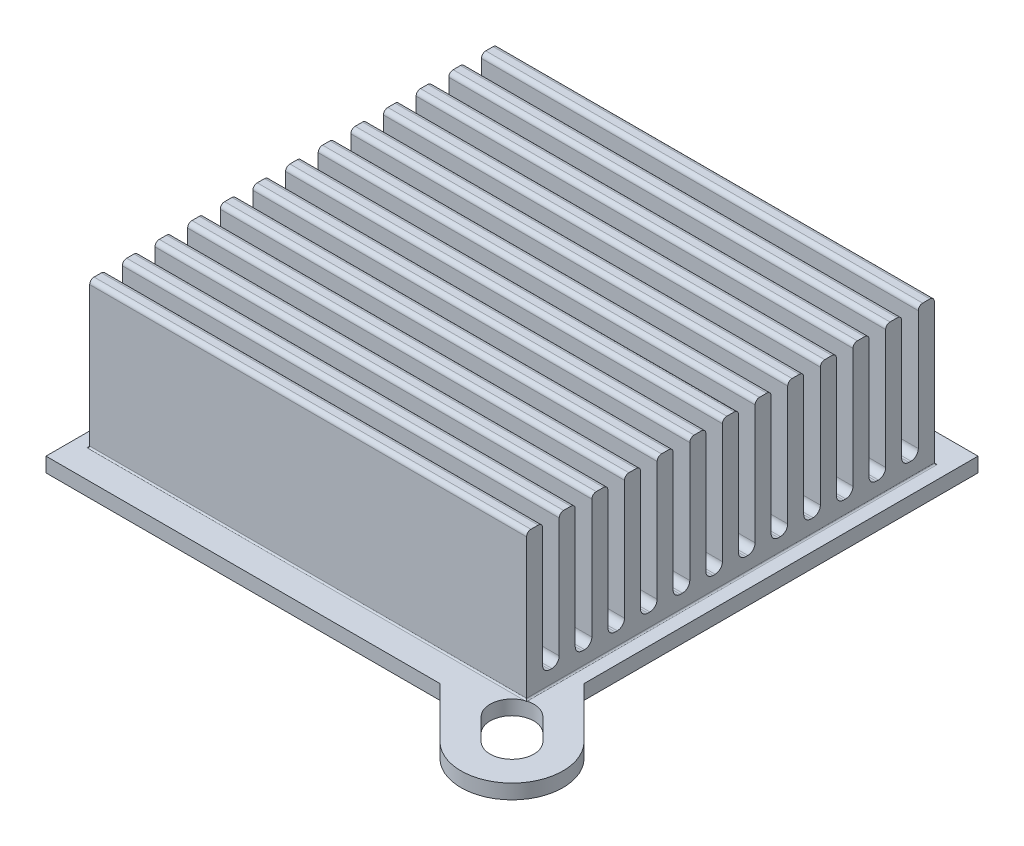
SolidWorks part; units mm, degrees
ref_plane "Płaszczyzna przednia" through (0, 0, 0) normal (0, 0, 1) x (1, 0, 0)
ref_plane "Płaszczyzna górna" through (0, 0, 0) normal (0, 1, 0) x (1, 0, 0)
ref_plane "Płaszczyzna prawa" through (0, 0, 0) normal (1, 0, 0) x (0, 0, -1)
sketch "Szkic1" plane through (0, 0, 0) normal (0, 1, 0) x (1, 0, 0)
  line L5 (-16, -16) -> (16, -16)
  line L6 (-16, -16) -> (-16, 16)
  line L7 (-16, 16) -> (16, 16)
  line L8 (16, -16) -> (16, 16)
  line L9 (-16, -16) -> (16, 16) construction
  line L10 (-16, 16) -> (16, -16) construction
  line L14 (-19.4454, 19.4454) -> (-5.5675, 33.3234) construction
  line L15 (19.4454, -19.4454) -> (38.3948, -0.496) construction
  line L16 (-19.4454, 19.4454) -> (19.4454, -19.4454) construction
  line L17 (-14.4957, 19.4454) -> (19.4454, -14.4957)
  line L18 (-19.4454, 14.4957) -> (14.4957, -19.4454)
  arc A2 (-14.4957, 19.4454) -> (-19.4454, 14.4957) centre (-16.9706, 16.9706) ccw
  arc A3 (14.4957, -19.4454) -> (19.4454, -14.4957) centre (16.9706, -16.9706) ccw
  point P0 (0, 0)
  dimension "D5" = 7
  dimension "D6" = 7
  dimension "D1" = 32
  dimension "D2" = 32
  dimension "D3" = 55
  dimension "D4" = 27.5
extrude "Dodanie-wyciągnięcie2" add sketch "Szkic1" along normal blind 1
sketch "Szkic2" plane through (0, 1, 0) normal (0, 1, 0) x (1, 0, 0)
  line L0 (-16, -16) -> (-16, 11.0503) construction
  line L1 (-15, 12.9) -> (15, 12.9)
  line L2 (-15, 12.9) -> (-15, 14)
  line L3 (-15, 14) -> (15, 14)
  line L4 (15, 12.9) -> (15, 14)
  line L5 (-15, 11.7583) -> (15, 11.7583)
  line L6 (-15, 10.6583) -> (15, 10.6583)
  line L7 (-15, 10.6583) -> (-15, 11.7583)
  line L8 (15, 10.6583) -> (15, 11.7583)
  line L9 (-15, 9.5167) -> (15, 9.5167)
  line L10 (-15, 8.4167) -> (15, 8.4167)
  line L11 (-15, 8.4167) -> (-15, 9.5167)
  line L12 (15, 8.4167) -> (15, 9.5167)
  line L13 (-15, 7.275) -> (15, 7.275)
  line L14 (-15, 6.175) -> (15, 6.175)
  line L15 (-15, 6.175) -> (-15, 7.275)
  line L16 (15, 6.175) -> (15, 7.275)
  line L17 (-15, 5.0333) -> (15, 5.0333)
  line L18 (-15, 3.9333) -> (15, 3.9333)
  line L19 (-15, 3.9333) -> (-15, 5.0333)
  line L20 (15, 3.9333) -> (15, 5.0333)
  line L21 (-15, 2.7917) -> (15, 2.7917)
  line L22 (-15, 1.6917) -> (15, 1.6917)
  line L23 (-15, 1.6917) -> (-15, 2.7917)
  line L24 (15, 1.6917) -> (15, 2.7917)
  line L25 (-15, 0.55) -> (15, 0.55)
  line L26 (-15, -0.55) -> (15, -0.55)
  line L27 (-15, -0.55) -> (-15, 0.55)
  line L28 (15, -0.55) -> (15, 0.55)
  line L29 (-15, -1.6917) -> (15, -1.6917)
  line L30 (-15, -2.7917) -> (15, -2.7917)
  line L31 (-15, -2.7917) -> (-15, -1.6917)
  line L32 (15, -2.7917) -> (15, -1.6917)
  line L33 (-15, -3.9333) -> (15, -3.9333)
  line L34 (-15, -5.0333) -> (15, -5.0333)
  line L35 (-15, -5.0333) -> (-15, -3.9333)
  line L36 (15, -5.0333) -> (15, -3.9333)
  line L37 (-15, -6.175) -> (15, -6.175)
  line L38 (-15, -7.275) -> (15, -7.275)
  line L39 (-15, -7.275) -> (-15, -6.175)
  line L40 (15, -7.275) -> (15, -6.175)
  line L41 (-15, -8.4167) -> (15, -8.4167)
  line L42 (-15, -9.5167) -> (15, -9.5167)
  line L43 (-15, -9.5167) -> (-15, -8.4167)
  line L44 (15, -9.5167) -> (15, -8.4167)
  line L45 (-15, -10.6583) -> (15, -10.6583)
  line L46 (-15, -11.7583) -> (15, -11.7583)
  line L47 (-15, -11.7583) -> (-15, -10.6583)
  line L48 (15, -11.7583) -> (15, -10.6583)
  line L49 (-15, -12.9) -> (15, -12.9)
  line L50 (-15, -14) -> (15, -14)
  line L51 (-15, -14) -> (-15, -12.9)
  line L52 (15, -14) -> (15, -12.9)
  line L53 (-11.0503, 16) -> (16, 16) construction
  line L54 (-16, -16) -> (11.0503, -16) construction
  dimension "D1" = 30
  dimension "D2" = 1
  dimension "D3" = 1.1
  dimension "D5" = 2
  dimension "D6" = 2
  dimension "D4" = 13
sketch "Szkic3" plane through (0, 1, 0) normal (0, 1, 0) x (1, 0, 0)
  line L1 (-15, 14) -> (15, 14)
  line L2 (-15, 14) -> (-15, -14)
  line L3 (-15, -14) -> (15, -14)
  line L4 (15, 14) -> (15, -14)
extrude "Dodanie-wyciągnięcie3" add sketch "Szkic3" along normal blind 1
extrude "Dodanie-wyciągnięcie4" add sketch "Szkic2" along normal blind 10
fillet "Zaokrąglenie1" radius 0.1 4 edges at (15, 1, 0) (0, 1, -14) (0, 1, 14) (-15, 1, 0)
fillet "Zaokrąglenie3" radius 0.5 24 edges at (0, 2, 12.9) (0, 2, 10.6583) (0, 2, 11.7583) (0, 2, 8.4167) (0, 2, 9.5167) (0, 2, 6.175) (0, 2, 7.275) (0, 2, 3.9333) (0, 2, 5.0333) (0, 2, 1.6917) (0, 2, 2.7917) (0, 2, -0.55) (0, 2, 0.55) (0, 2, -2.7917) (0, 2, -1.6917) (0, 2, -5.0333) (0, 2, -3.9333) (0, 2, -7.275) (0, 2, -6.175) (0, 2, -9.5167) (0, 2, -8.4167) (0, 2, -10.6583) (0, 2, -11.7583) (0, 2, -12.9)
fillet "Zaokrąglenie4" radius 0.3 26 edges at (0, 11, 14) (0, 11, 12.9) (0, 11, 11.7583) (0, 11, 10.6583) (0, 11, 9.5167) (0, 11, 8.4167) (0, 11, 7.275) (0, 11, 6.175) (0, 11, 5.0333) (0, 11, 3.9333) (0, 11, 2.7917) (0, 11, 1.6917) (0, 11, 0.55) (0, 11, -0.55) (0, 11, -1.6917) (0, 11, -2.7917) (0, 11, -3.9333) (0, 11, -5.0333) (0, 11, -6.175) (0, 11, -7.275) (0, 11, -8.4167) (0, 11, -9.5167) (0, 11, -10.6583) (0, 11, -11.7583) (0, 11, -12.9) (0, 11, -14)
sketch "Szkic4" plane through (0, 1, 0) normal (0, 1, 0) x (1, 0, 0)
  line L0 (-16.9706, 16.9706) -> (-15.4998, 15.4998) construction
  line L1 (-15.9099, 18.0312) -> (-14.4391, 16.5604)
  line L2 (-18.0312, 15.9099) -> (-16.5604, 14.4391)
  line L3 (16.9706, -16.9706) -> (15.4998, -15.4998) construction
  line L5 (15.9099, -18.0312) -> (14.4391, -16.5604)
  line L6 (18.0312, -15.9099) -> (16.5604, -14.4391)
  line L7 (-14.4957, 19.4454) -> (-11.0503, 16) construction
  line L8 (16, -11.0503) -> (19.4454, -14.4957) construction
  line L9 (-19.4454, 19.4454) -> (19.4454, -19.4454) construction
  arc A0 (-15.9099, 18.0312) -> (-18.0312, 15.9099) centre (-16.9706, 16.9706) ccw
  arc A1 (-16.5604, 14.4391) -> (-14.4391, 16.5604) centre (-15.4998, 15.4998) ccw
  arc A2 (15.9099, -18.0312) -> (18.0312, -15.9099) centre (16.9706, -16.9706) ccw
  arc A3 (16.5604, -14.4391) -> (14.4391, -16.5604) centre (15.4998, -15.4998) ccw
  arc A4 (-14.4957, 19.4454) -> (-19.4454, 14.4957) centre (-16.9706, 16.9706) ccw construction
  arc A5 (14.4957, -19.4454) -> (19.4454, -14.4957) centre (16.9706, -16.9706) ccw construction
  point P3 (-16.2352, 16.2352)
  point P13 (16.2352, -16.2352)
  point P28 (0, 0)
  dimension "D1" = 2
  dimension "D2" = 2
  dimension "D3" = 43.84
  dimension "D4" = 21.92
extrude "Wytnij-wyciągnięcie1" cut sketch "Szkic4" against normal through all contours L2 A1 L1 A0 | L6 A3 L5 A2
equation "\"D2@Szkic1\"=\"D1@Szkic1\""
equation "\"D4@Szkic1\"=\"D3@Szkic1\"/2"
equation "\"D6@Szkic1\"=\"D5@Szkic1\""
equation "\"D6@Szkic2\"=\"D5@Szkic2\""
equation "\"D4@Szkic4\"=\"D3@Szkic4\"/2"
